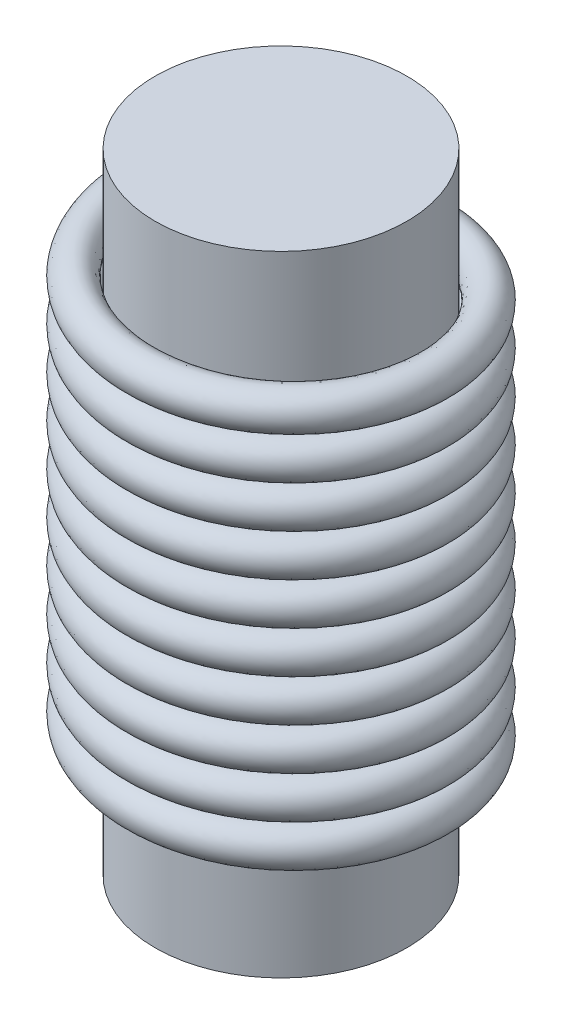
SolidWorks part; units mm, degrees
ref_plane "Front Plane" through (0, 0, 0) normal (0, 0, 1) x (1, 0, 0)
ref_plane "Top Plane" through (0, 0, 0) normal (0, 1, 0) x (1, 0, 0)
ref_plane "Right Plane" through (0, 0, 0) normal (1, 0, 0) x (0, 0, -1)
sketch "Sketch1" plane through (0, 0, 0) normal (0, 1, 0) x (1, 0, 0)
  circle A0 centre (0, 0) radius 3
  dimension "D1" = 6
extrude "Boss-Extrude1" add sketch "Sketch1" along normal blind 12.5 and the other way blind 2.5
sketch "Sketch2" plane through (0, 0, 0) normal (0, 1, 0) x (1, 0, 0)
  circle A0 centre (0, 0) radius 3.5
  dimension "D1" = 7
curve "Helix/Spiral1" pitch 1 height 10 turns 10
sketch "Sketch3" plane through (0, 0, 0) normal (0, 0, 1) x (1, 0, 0)
  circle A0 centre (-3.5, 0) radius 0.45
  spline S0 degree 3 poles (-3.5, 0) (-3.5, 0.0207) (-3.3178, 0.0626) (-2.5393, 0.125) (-1.3743, 0.1875) (0, 0.25) (1.3743, 0.3125) (2.5393, 0.375) (3.3178, 0.4375) (3.5911, 0.5) (3.3178, 0.5625) (2.5393, 0.625) (1.3743, 0.6875) (0, 0.75) (-1.3743, 0.8125) (-2.5393, 0.875) (-3.3178, 0.9375) (-3.5911, 1) (-3.3178, 1.0625) (-2.5393, 1.125) (-1.3743, 1.1875) (0, 1.25) (1.3743, 1.3125) (2.5393, 1.375) (3.3178, 1.4375) (3.5911, 1.5) (3.3178, 1.5625) (2.5393, 1.625) (1.3743, 1.6875) (0, 1.75) (-1.3743, 1.8125) (-2.5393, 1.875) (-3.3178, 1.9375) (-3.5911, 2) (-3.3178, 2.0625) (-2.5393, 2.125) (-1.3743, 2.1875) (0, 2.25) (1.3743, 2.3125) (2.5393, 2.375) (3.3178, 2.4375) (3.5911, 2.5) (3.3178, 2.5625) (2.5393, 2.625) (1.3743, 2.6875) (0, 2.75) (-1.3743, 2.8125) (-2.5393, 2.875) (-3.3178, 2.9375) (-3.5911, 3) (-3.3178, 3.0625) (-2.5393, 3.125) (-1.3743, 3.1875) (0, 3.25) (1.3743, 3.3125) (2.5393, 3.375) (3.3178, 3.4375) (3.5911, 3.5) (3.3178, 3.5625) (2.5393, 3.625) (1.3743, 3.6875) (0, 3.75) (-1.3743, 3.8125) (-2.5393, 3.875) (-3.3178, 3.9375) (-3.5911, 4) (-3.3178, 4.0625) (-2.5393, 4.125) (-1.3743, 4.1875) (0, 4.25) (1.3743, 4.3125) (2.5393, 4.375) (3.3178, 4.4375) (3.5911, 4.5) (3.3178, 4.5625) (2.5393, 4.625) (1.3743, 4.6875) (0, 4.75) (-1.3743, 4.8125) (-2.5393, 4.875) (-3.3178, 4.9375) (-3.5911, 5) (-3.3178, 5.0625) (-2.5393, 5.125) (-1.3743, 5.1875) (0, 5.25) (1.3743, 5.3125) (2.5393, 5.375) (3.3178, 5.4375) (3.5911, 5.5) (3.3178, 5.5625) (2.5393, 5.625) (1.3743, 5.6875) (0, 5.75) (-1.3743, 5.8125) (-2.5393, 5.875) (-3.3178, 5.9375) (-3.5911, 6) (-3.3178, 6.0625) (-2.5393, 6.125) (-1.3743, 6.1875) (0, 6.25) (1.3743, 6.3125) (2.5393, 6.375) (3.3178, 6.4375) (3.5911, 6.5) (3.3178, 6.5625) (2.5393, 6.625) (1.3743, 6.6875) (0, 6.75) (-1.3743, 6.8125) (-2.5393, 6.875) (-3.3178, 6.9375) (-3.5911, 7) (-3.3178, 7.0625) (-2.5393, 7.125) (-1.3743, 7.1875) (0, 7.25) (1.3743, 7.3125) (2.5393, 7.375) (3.3178, 7.4375) (3.5911, 7.5) (3.3178, 7.5625) (2.5393, 7.625) (1.3743, 7.6875) (0, 7.75) (-1.3743, 7.8125) (-2.5393, 7.875) (-3.3178, 7.9375) (-3.5911, 8) (-3.3178, 8.0625) (-2.5393, 8.125) (-1.3743, 8.1875) (0, 8.25) (1.3743, 8.3125) (2.5393, 8.375) (3.3178, 8.4375) (3.5911, 8.5) (3.3178, 8.5625) (2.5393, 8.625) (1.3743, 8.6875) (0, 8.75) (-1.3743, 8.8125) (-2.5393, 8.875) (-3.3178, 8.9375) (-3.5911, 9) (-3.3178, 9.0625) (-2.5393, 9.125) (-1.3743, 9.1875) (0, 9.25) (1.3743, 9.3125) (2.5393, 9.375) (3.3178, 9.4375) (3.5911, 9.5) (3.3178, 9.5625) (2.5393, 9.625) (1.3743, 9.6875) (0, 9.75) (-1.3743, 9.8125) (-2.5393, 9.875) (-3.3178, 9.9374) (-3.5, 9.9793) (-3.5, 10) knots 0 0 0 0 0.00625 0.0125 0.01875 0.025 0.03125 0.0375 0.04375 0.05 0.05625 0.0625 0.06875 0.075 0.08125 0.0875 0.09375 0.1 0.10625 0.1125 0.11875 0.125 0.13125 0.1375 0.14375 0.15 0.15625 0.1625 0.16875 0.175 0.18125 0.1875 0.19375 0.2 0.20625 0.2125 0.21875 0.225 0.23125 0.2375 0.24375 0.25 0.25625 0.2625 0.26875 0.275 0.28125 0.2875 0.29375 0.3 0.30625 0.3125 0.31875 0.325 0.33125 0.3375 0.34375 0.35 0.35625 0.3625 0.36875 0.375 0.38125 0.3875 0.39375 0.4 0.40625 0.4125 0.41875 0.425 0.43125 0.4375 0.44375 0.45 0.45625 0.4625 0.46875 0.475 0.48125 0.4875 0.49375 0.5 0.50625 0.5125 0.51875 0.525 0.53125 0.5375 0.54375 0.55 0.55625 0.5625 0.56875 0.575 0.58125 0.5875 0.59375 0.6 0.60625 0.6125 0.61875 0.625 0.63125 0.6375 0.64375 0.65 0.65625 0.6625 0.66875 0.675 0.68125 0.6875 0.69375 0.7 0.70625 0.7125 0.71875 0.725 0.73125 0.7375 0.74375 0.75 0.75625 0.7625 0.76875 0.775 0.78125 0.7875 0.79375 0.8 0.80625 0.8125 0.81875 0.825 0.83125 0.8375 0.84375 0.85 0.85625 0.8625 0.86875 0.875 0.88125 0.8875 0.89375 0.9 0.90625 0.9125 0.91875 0.925 0.93125 0.9375 0.94375 0.95 0.95625 0.9625 0.96875 0.975 0.98125 0.9875 0.99375 1 1 1 1 construction
  dimension "D1" = 0.9
sweep "Sweep1" add profiles "Sketch3" path "Helix/Spiral1"
